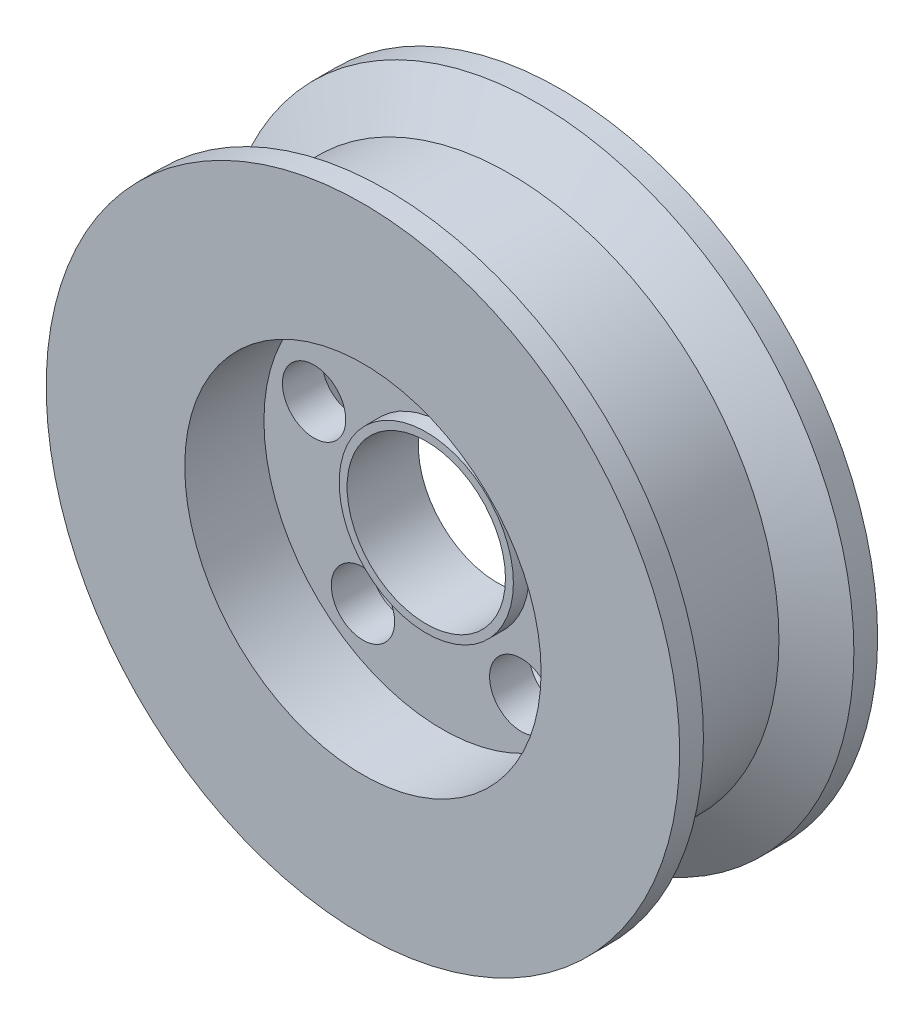
SolidWorks part; units mm, degrees
ref_plane "Front Plane" through (0, 0, 0) normal (0, 0, 1) x (1, 0, 0)
ref_plane "Top Plane" through (0, 0, 0) normal (0, 1, 0) x (1, 0, 0)
ref_plane "Right Plane" through (0, 0, 0) normal (1, 0, 0) x (0, 0, -1)
sketch "Sketch1" plane through (0, 0, 0) normal (0, 0, 1) x (1, 0, 0)
  circle A0 centre (0, 0) radius 10
  circle A1 centre (0, 0) radius 40
  dimension "D1" = 20
  dimension "D2" = 80
extrude "Boss-Extrude1" add sketch "Sketch1" along normal mid plane 25
sketch "Sketch2" plane through (0, 0, 12.5) normal (0, 0, 1) x (1, 0, 0)
  circle A0 centre (0, 0) radius 22.5
  circle A1 centre (0, 0) radius 40 construction
  dimension "D1" = 17.5
extrude "Cut-Extrude1" cut sketch "Sketch2" against normal blind 10
mirror "Mirror1" about plane through (0, 0, 0) normal (0, 0, 1) of "Cut-Extrude1"
sketch "Sketch3" plane through (0, 0, 2.5) normal (0, 0, 1) x (1, 0, 0)
  circle A0 centre (0, 17) radius 4
  dimension "D1" = 8
  dimension "D2" = 17
extrude "Cut-Extrude2" cut sketch "Sketch3" against normal through all
pattern_circular "CirPattern1" count 5 over 360 about axis through (0, 0, 0) along (0, 0, 1) of "Cut-Extrude2"
sketch "Sketch4" plane through (0, 0, 2.5) normal (0, 0, 1) x (1, 0, 0)
  circle A0 centre (0, 0) radius 11
  circle A1 centre (0, 0) radius 10 construction
  circle A2 centre (0, 0) radius 10
  dimension "D1" = 22
extrude "Boss-Extrude2" add sketch "Sketch4" along normal blind 2 and the other way blind 7
sketch "Sketch5" plane through (0, 0, 0) normal (0, 1, 0) x (1, 0, 0)
  line L0 (0, 0) -> (0, 50) construction
  line L1 (-40, 9.5) -> (-40, -9.5)
  line L2 (-40, 12.5) -> (-40, -12.5) construction
  line L3 (-40, -9.5) -> (-34, -6.0361)
  line L4 (-34, -6.0361) -> (-34, 6.0359)
  line L5 (-34, 6.0359) -> (-40, 9.5)
  point P9 (0, 0)
  point P12 (0, 0)
  dimension "D1" = 3
  dimension "D2" = 3
  dimension "D3" = 6
  dimension "D4" = 60.001
  dimension "D5" = 60
revolve "Cut-Revolve1" cut sketch "Sketch5" angle 360 about L0
